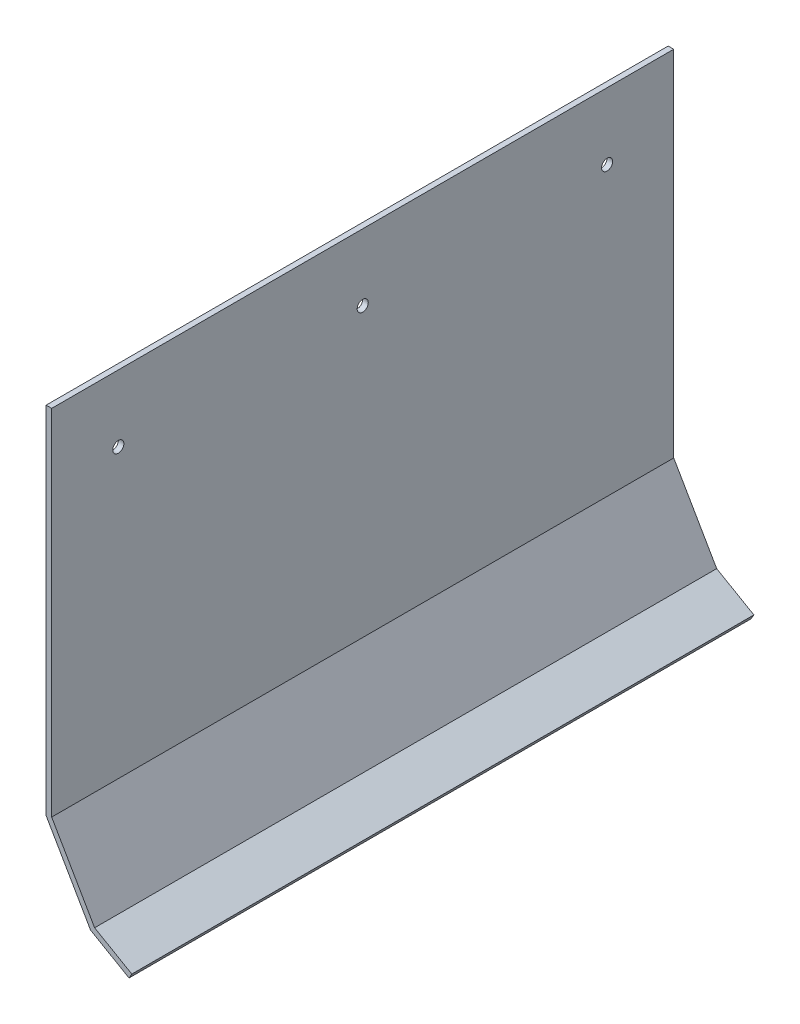
SolidWorks part; units mm, degrees
ref_plane "Front" through (0, 0, 0) normal (0, 0, 1) x (1, 0, 0)
ref_plane "Top" through (0, 0, 0) normal (0, 1, 0) x (1, 0, 0)
ref_plane "Right" through (0, 0, 0) normal (1, 0, 0) x (0, 0, -1)
sketch "스케치1" plane through (0, 0, 0) normal (0, 0, 1) x (1, 0, 0)
  line L0 (-34.4421, -34.1691) -> (-21.7421, -56.1661)
  line L1 (-34.4421, 67.4309) -> (-32.8546, 67.4309)
  line L2 (-34.4421, 67.4309) -> (-34.4421, -34.1691)
  line L4 (-32.8546, 67.4309) -> (-32.8546, -33.7437)
  line L5 (-21.7421, -56.1661) -> (-10.7436, -62.5161)
  line L6 (-10.7436, -62.5161) -> (-9.9498, -61.1413)
  line L7 (-9.9498, -61.1413) -> (-20.5799, -55.004)
  line L8 (-20.5799, -55.004) -> (-32.8546, -33.7437)
  point P1 (-26.7173, -44.3739)
  dimension "D1" = 1.5875
  dimension "D2" = 1.5875
  dimension "D3" = 1.5875
  dimension "D4" = 101.6
  dimension "D5" = 25.4
  dimension "D6" = 12.7
  dimension "D7" = 150
  dimension "D8" = 150
extrude "보스-돌출1" add sketch "스케치1" along normal blind 177.8
sketch "스케치2" plane through (-34.4421, 0, 0) normal (-1, 0, 0) x (0, 0, 1)
  line L0 (0, 67.4309) -> (0, -34.1691) construction
  line L1 (177.8, 67.4309) -> (177.8, -34.1691) construction
  line L2 (177.8, 67.4309) -> (0, 67.4309) construction
  circle A0 centre (158.75, 48.3809) radius 1.5875
  circle A2 centre (88.9, 48.3809) radius 1.5875
  circle A3 centre (19.05, 48.3809) radius 1.5875
  dimension "D1" = 19.05
  dimension "D5" = 3.175
  dimension "D6" = 3.175
  dimension "D8" = 3.175
  dimension "D2" = 88.9
  dimension "D4" = 19.05
  dimension "D9" = 19.05
  dimension "D11" = 19.05
  dimension "D12" = 19.05
extrude "컷-돌출1" cut sketch "스케치2" against normal blind 254
